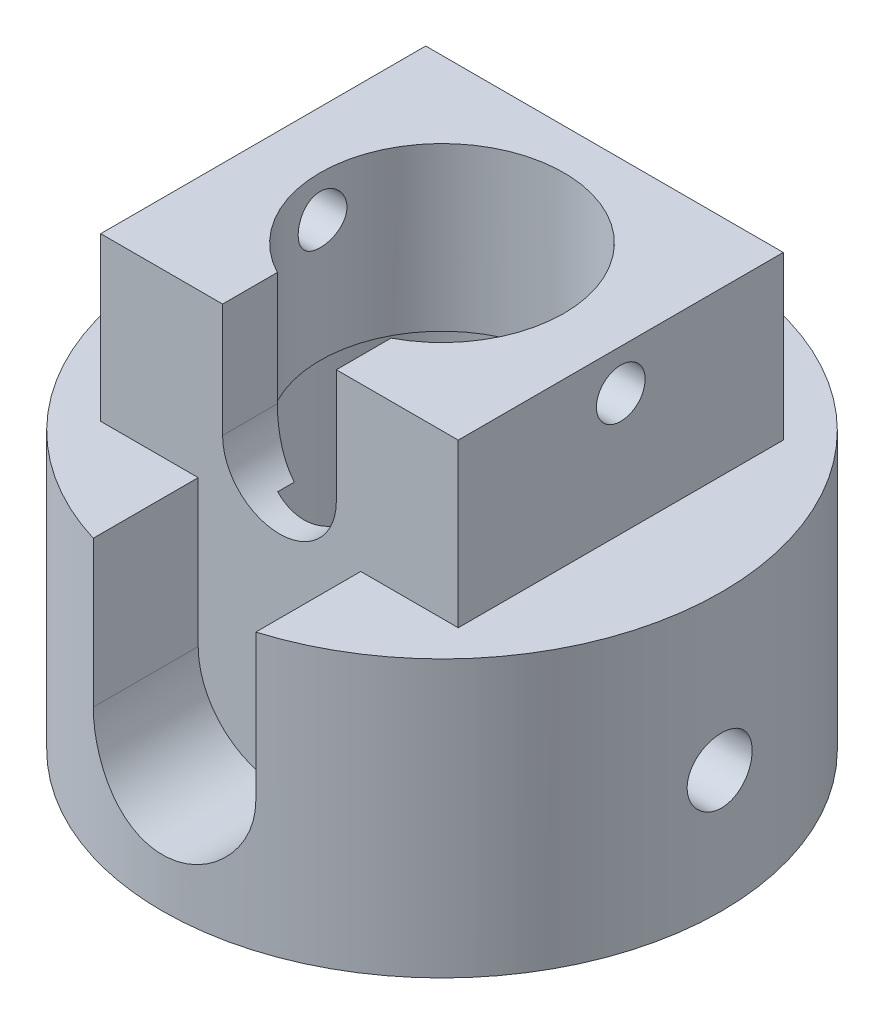
SolidWorks part; units mm, degrees
ref_plane "Front Plane" through (0, 0, 0) normal (0, 0, 1) x (1, 0, 0)
ref_plane "Top Plane" through (0, 0, 0) normal (0, 1, 0) x (1, 0, 0)
ref_plane "Right Plane" through (0, 0, 0) normal (1, 0, 0) x (0, 0, -1)
sketch "Sketch1" plane through (0, 0, 0) normal (0, 1, 0) x (1, 0, 0)
  circle A0 centre (0, 0) radius 8.5
  circle A1 centre (0, 0) radius 17.2
  dimension "D1" = 17
  dimension "D2" = 34.4
extrude "Boss-Extrude1" add sketch "Sketch1" along normal blind 17
sketch "Sketch2" plane through (0, 17, 0) normal (0, 1, 0) x (1, 0, 0)
  line L1 (-11, -10) -> (11, -10)
  line L2 (-11, -10) -> (-11, 10)
  line L3 (-11, 10) -> (11, 10)
  line L4 (11, -10) -> (11, 10)
  line L5 (-11, -10) -> (11, 10) construction
  line L6 (-11, 10) -> (11, -10) construction
  circle A0 centre (0, 0) radius 7.5
  point P0 (0, 0)
  dimension "D3" = 15
  dimension "D1" = 22
  dimension "D2" = 20
extrude "Boss-Extrude2" add sketch "Sketch2" along normal blind 10 contours L3 L4 L1 L2 | A0
sketch "Sketch3" plane through (11, 0, 0) normal (1, 0, 0) x (0, 0, -1)
  line L0 (0, 0) -> (0, 27) construction
  line L1 (-10, 27) -> (10, 27) construction
  circle A0 centre (0, 24.5) radius 1.5
  dimension "D1" = 3
  dimension "D2" = 2.5
extrude "Cut-Extrude1" cut sketch "Sketch3" against normal up to surface (22 mm away) up to face at (-11, 22, 0)
sketch "Sketch4" plane through (0, 0, 0) normal (1, 0, 0) x (0, 0, -1)
  line L0 (0, 0) -> (0, 16.9495) construction
  line L1 (0, 14.85) -> (0, -14.85) construction
  line L2 (-17.2, 0) -> (17.2, 0) construction
  circle A0 centre (0, 7.5) radius 2
  dimension "D1" = 4
  dimension "D2" = 7.5
extrude "Cut-Extrude2" cut sketch "Sketch4" along normal blind 20
sketch "Sketch5" plane through (0, 0, 10) normal (0, 0, 1) x (1, 0, 0)
  line L0 (0, 0) -> (0, 17) construction
  line L1 (-11, 17) -> (11, 17) construction
  line L2 (-5, 17) -> (5, 17)
  line L3 (17.2, 17) -> (-17.2, 17) construction
  line L4 (-5, 17) -> (-5, 8)
  line L5 (0, 8) -> (-4.7853, 8) construction
  line L6 (5, 17) -> (5, 8)
  arc A0 (-5, 8) -> (5, 8) centre (0, 8) ccw
  dimension "D1" = 5
  dimension "D2" = 9
extrude "Cut-Extrude3" cut sketch "Sketch5" along normal blind 20
sketch "Sketch6" plane through (0, 0, 10) normal (0, 0, 1) x (1, 0, 0)
  line L0 (0, 0) -> (0, 27) construction
  line L1 (-17.2, 0) -> (17.2, 0) construction
  line L2 (-11, 27) -> (11, 27) construction
  line L3 (3.5, 27) -> (-3.5, 27)
  line L4 (-3.5, 27) -> (-3.5, 20)
  line L5 (0, 20) -> (-3.5, 20) construction
  line L6 (3.5, 27) -> (3.5, 20)
  arc A0 (-3.5, 20) -> (3.5, 20) centre (0, 20) ccw
  dimension "D1" = 3.5
  dimension "D2" = 7
extrude "Cut-Extrude4" cut sketch "Sketch6" against normal blind 5
